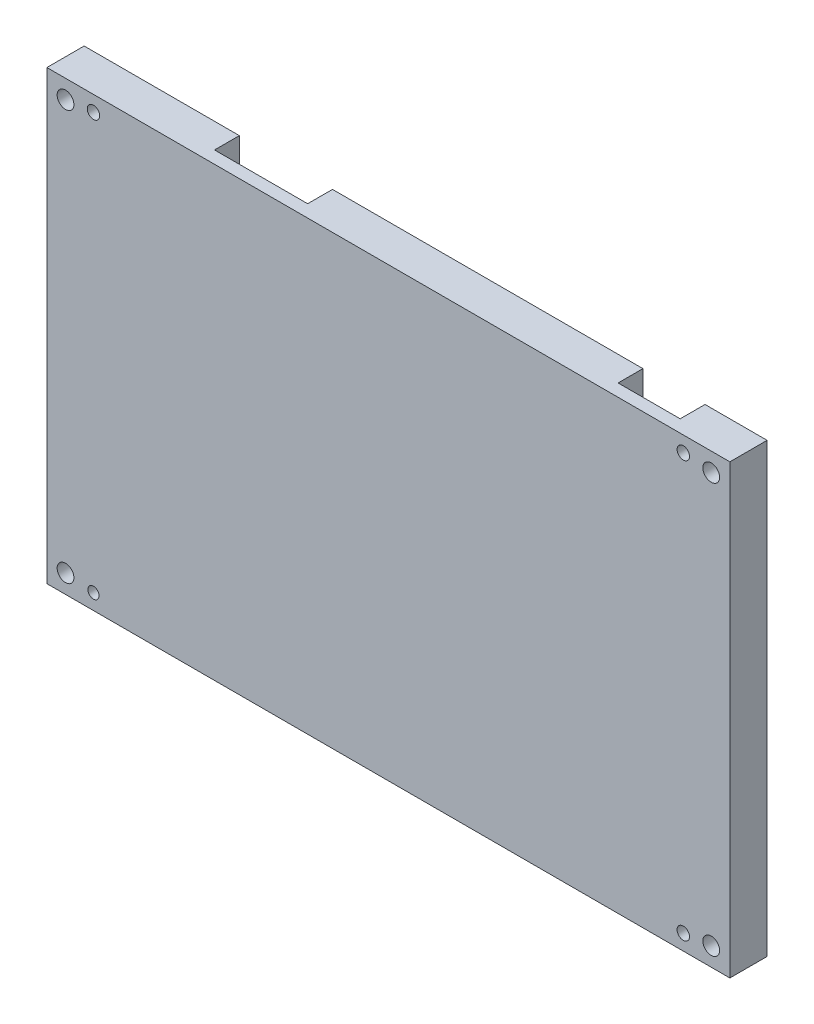
SolidWorks part; units mm, degrees
ref_plane "Plan de face" through (0, 0, 0) normal (0, 0, 1) x (1, 0, 0)
ref_plane "Plan de dessus" through (0, 0, 0) normal (0, 1, 0) x (1, 0, 0)
ref_plane "Plan de droite" through (0, 0, 0) normal (1, 0, 0) x (0, 0, -1)
sketch "Main-Sketch" plane through (0, 0, 0) normal (0, 0, 1) x (1, 0, 0)
  line L1 (0, 0) -> (110, 0)
  line L2 (0, 0) -> (0, 72)
  line L3 (0, 72) -> (110, 72)
  line L4 (110, 0) -> (110, 72)
  dimension "D1" = 110
  dimension "D2" = 72
extrude "Main-Extrusion" add sketch "Main-Sketch" along normal blind 6
sketch "Main-Hole-Sketch" plane through (0, 0, 6) normal (0, 0, 1) x (1, 0, 0)
  line L0 (0, 72) -> (0, 0) construction
  line L2 (0, 0) -> (110, 0) construction
  line L3 (110, 0) -> (110, 72) construction
  line L4 (110, 72) -> (0, 72) construction
  circle A0 centre (7.5, 69.5) radius 1
  circle A1 centre (7.5, 2.5) radius 0.9
  circle A2 centre (102.5, 2.5) radius 1
  circle A3 centre (102.5, 69.5) radius 1
  dimension "D1" = 2
  dimension "D2" = 1.8
  dimension "D3" = 2
  dimension "D4" = 2
  dimension "D6" = 2.5
  dimension "D5" = 7.5
  dimension "D7" = 2.5
  dimension "D8" = 7.5
extrude "Main-Hole" cut sketch "Main-Hole-Sketch" against normal through all
sketch "Epia-Fix-Sketch" plane through (0, 0, 0) normal (0, 0, 1) x (1, 0, 0)
  line L0 (0, 72) -> (0, 0) construction
  line L1 (5, 47) -> (82, 47)
  line L2 (5, 47) -> (5, 7)
  line L3 (5, 7) -> (82, 7)
  line L4 (82, 47) -> (82, 7)
  line L5 (0, 0) -> (110, 0) construction
  line L6 (110, 72) -> (0, 72) construction
  line L7 (25, 72) -> (40, 72)
  line L8 (25, 72) -> (25, 64)
  line L9 (25, 64) -> (40, 64)
  line L10 (40, 72) -> (40, 64)
  line L11 (110, 0) -> (110, 72) construction
  line L12 (100, 72) -> (90, 72)
  line L13 (100, 72) -> (100, 64)
  line L14 (100, 64) -> (90, 64)
  line L15 (90, 72) -> (90, 64)
  line L17 (94, 23) -> (102, 23)
  line L18 (94, 23) -> (94, 39)
  line L19 (94, 39) -> (102, 39)
  line L20 (102, 23) -> (102, 39)
  dimension "D1" = 5
  dimension "D2" = 77
  dimension "D3" = 7
  dimension "D4" = 40
  dimension "D5" = 8
  dimension "D6" = 25
  dimension "D7" = 15
  dimension "D8" = 10
  dimension "D9" = 10
  dimension "D10" = 33
  dimension "D11" = 16
  dimension "D12" = 8
  dimension "D13" = 8
extrude "Epia-Fix" cut sketch "Epia-Fix-Sketch" along normal blind 4
sketch "Fix-Sketch" plane through (0, 0, 6) normal (0, 0, 1) x (1, 0, 0)
  line L0 (110, 0) -> (110, 72) construction
  line L1 (110, 72) -> (0, 72) construction
  line L2 (0, 0) -> (110, 0) construction
  line L3 (0, 72) -> (0, 0) construction
  circle A0 centre (107, 69) radius 1.35
  circle A1 centre (107, 3) radius 1.35
  circle A2 centre (3, 69) radius 1.35
  circle A3 centre (3, 3) radius 1.35
  dimension "D1" = 2.7
  dimension "D2" = 3
  dimension "D3" = 3
  dimension "D4" = 3
  dimension "D5" = 3
extrude "Fix-Hole" cut sketch "Fix-Sketch" against normal through all
